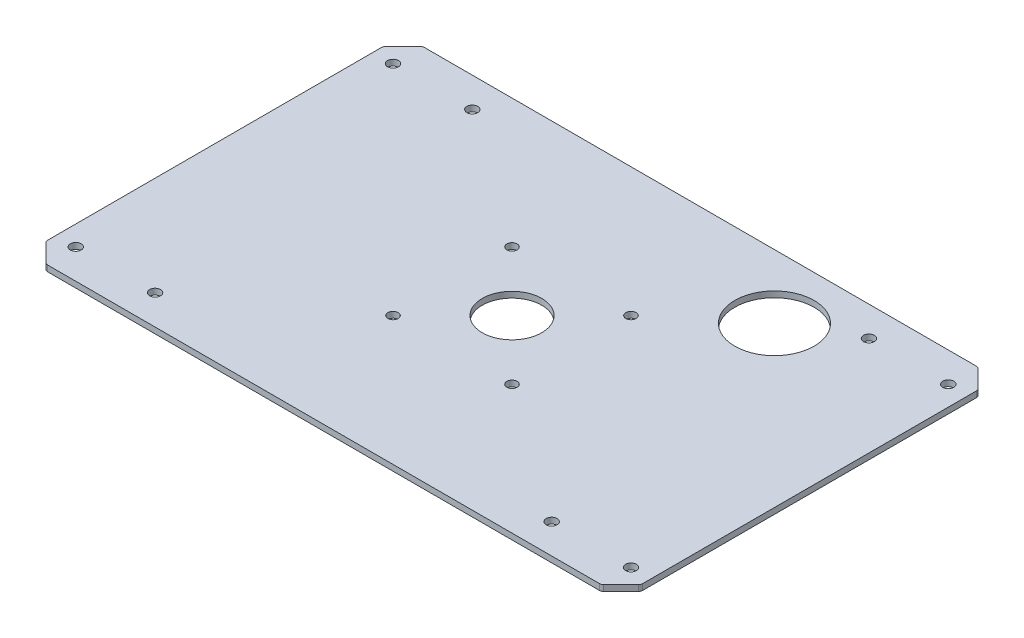
SolidWorks part; units mm, degrees
ref_plane "Plan de face" through (0, 0, 0) normal (0, 0, 1) x (1, 0, 0)
ref_plane "Plan de dessus" through (0, 0, 0) normal (0, 1, 0) x (1, 0, 0)
ref_plane "Plan de droite" through (0, 0, 0) normal (1, 0, 0) x (0, 0, -1)
sketch "Esquisse1" plane through (0, 0, 0) normal (0, 1, 0) x (1, 0, 0)
  line L1 (-150, -95) -> (150, -95)
  line L2 (-150, -95) -> (-150, 95)
  line L3 (-150, 95) -> (150, 95)
  line L4 (150, -95) -> (150, 95)
  line L5 (-150, -95) -> (150, 95) construction
  line L6 (-150, 95) -> (150, -95) construction
  point P0 (0, 0)
  dimension "D1" = 300
  dimension "D2" = 190
extrude "Boss.-Extru.1" add sketch "Esquisse1" along normal blind 3
chamfer "Chanfrein1" distance 10 angle 45 4 edges at (-150, 1.5, 95) (150, 1.5, 95) (150, 1.5, -95) (-150, 1.5, -95)
fillet "Congé1" radius 2 8 edges at (-150, 1.5, -85) (-140, 1.5, -95) (140, 1.5, -95) (150, 1.5, -85) (150, 1.5, 85) (140, 1.5, 95) (-140, 1.5, 95) (-150, 1.5, 85)
sketch "Esquisse2" plane through (0, 0, 0) normal (0, -1, 0) x (1, 0, 0)
  line L0 (-140, 80) -> (-100, 80) construction
  line L3 (-150, -84.1716) -> (-150, 84.1716) construction
  line L4 (-139.1716, 95) -> (139.1716, 95) construction
  circle A0 centre (-140, 80) radius 2.75
  circle A1 centre (-100, 80) radius 2.75
  point P4 (-120, 80)
  dimension "D1" = 5.5
  dimension "D2" = 40
  dimension "D3" = 10
  dimension "D4" = 15
extrude "Enlèv. mat.-Extru.1" cut sketch "Esquisse2" against normal through all
pattern_linear "Répétition linéaire1" count 2 spacing 240 along (1, 0, 0) count 2 spacing 160 along (0, 0, -1) of "Enlèv. mat.-Extru.1"
sketch "Esquisse4" plane through (0, 3, 0) normal (0, 1, 0) x (1, 0, 0)
  line L0 (59.1, 75) -> (80, 50.6) construction
  circle A0 centre (59.1, 75) radius 1.6 construction
  circle A1 centre (80, 50.6) radius 1.6 construction
  circle A2 centre (100, 80) radius 2.75 construction
  circle A3 centre (100, 80) radius 2.75
  circle A4 centre (69.55, 62.8) radius 20
  circle A6 centre (0, 0) radius 15
  point P7 (69.55, 62.8)
  dimension "D1" = 3.2
  dimension "D4" = 20
  dimension "D6" = 40
  dimension "D7" = 30
  dimension "D2" = 24.4
  dimension "D3" = 20.9
  dimension "D5" = 5
extrude "Enlèv. mat.-Extru.3" cut sketch "Esquisse4" against normal blind 10
sketch "Esquisse5" plane through (0, 3, 0) normal (0, 1, 0) x (1, 0, 0)
  line L1 (-30, -30) -> (30, -30) construction
  line L2 (-30, -30) -> (-30, 30) construction
  line L3 (-30, 30) -> (30, 30) construction
  line L4 (30, -30) -> (30, 30) construction
  line L5 (-30, -30) -> (30, 30) construction
  line L6 (-30, 30) -> (30, -30) construction
  circle A0 centre (-30, 30) radius 2.6
  circle A1 centre (30, 30) radius 2.6
  circle A2 centre (30, -30) radius 2.6
  circle A3 centre (-30, -30) radius 2.6
  point P0 (0, 0)
  dimension "D2" = 5.2
  dimension "D1" = 60
extrude "Enlèv. mat.-Extru.4" cut sketch "Esquisse5" against normal through all
